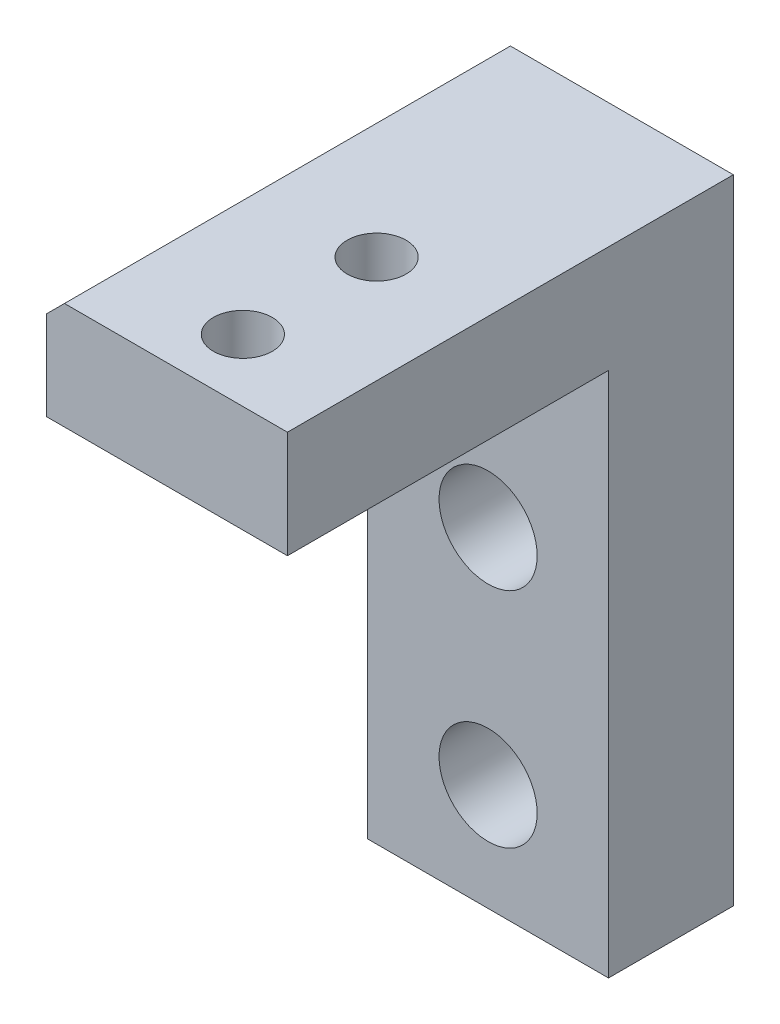
SolidWorks part; units mm, degrees
ref_plane "Front Plane" through (0, 0, 0) normal (0, 0, 1) x (1, 0, 0)
ref_plane "Top Plane" through (0, 0, 0) normal (0, 1, 0) x (1, 0, 0)
ref_plane "Right Plane" through (0, 0, 0) normal (1, 0, 0) x (0, 0, -1)
sketch "Sketch1" plane through (0, 0, 0) normal (0, 0, 1) x (1, 0, 0)
  line L1 (-17.6697, 16.1437) -> (-4.1697, 16.1437)
  line L2 (-17.6697, 16.1437) -> (-17.6697, -19.3563)
  line L3 (-17.6697, -19.3563) -> (-4.1697, -19.3563)
  line L4 (-4.1697, 16.1437) -> (-4.1697, -19.3563)
  circle A0 centre (-10.9197, -13.3563) radius 2.75
  circle A1 centre (-10.9197, -0.8563) radius 2.75
  point P8 (0, 0)
  point P9 (0, 0)
  dimension "D3" = 5.5
  dimension "D4" = 12.5
  dimension "D5" = 6
  dimension "D1" = 35.5
  dimension "D2" = 13.5
extrude "Boss-Extrude1" add sketch "Sketch1" along normal blind 7
sketch "Sketch2" plane through (0, 0, 7) normal (0, 0, 1) x (1, 0, 0)
  line L0 (-4.1697, -19.3563) -> (-4.1697, 16.1437) construction
  line L1 (-17.6697, 16.1437) -> (-4.1697, 16.1437)
  line L2 (-17.6697, 16.1437) -> (-17.6697, 10.1437)
  line L3 (-17.6697, 10.1437) -> (-4.1697, 10.1437)
  line L4 (-4.1697, 16.1437) -> (-4.1697, 10.1437)
  dimension "D1" = 6
extrude "Boss-Extrude2" add sketch "Sketch2" along normal blind 18
chamfer "Chamfer1" distance 1 angle 45 1 edges at (-17.6697, 16.1437, 12.5)
hole_wizard "M4x0.7 Tapped Hole1" positions "Sketch3" profile "Sketch4" tap size "M4x0.7" standard "ANSI Metric" end condition through all
sketch "Sketch3" plane through (0, 16.1437, 0) normal (0, 1, 0) x (1, 0, 0)
  line L0 (-4.1697, 0) -> (-16.6697, 0) construction
  line L1 (-17.6697, -25) -> (-17.6697, 0) construction
  point P0 (-10.1697, -21.5)
  point P2 (-10.1697, -14)
  dimension "D1" = 14
  dimension "D2" = 21.5
  dimension "D3" = 7.5
  dimension "D4" = 7.5
sketch "Sketch4" plane through (-10.1697, 16.1437, 21.5) normal (1, 0, 0) x (0, 0, 1)
  line L0 (0, 0) -> (0, 35.5)
  line L1 (0, 35.5) -> (1.65, 35.5)
  line L2 (1.65, 35.5) -> (1.65, 0)
  line L5 (1.65, 0) -> (0, 0)
  line L11 (0, -6.35) -> (0, 107.95) construction
  dimension "Thru Tap Drill Dia." = 3.3
  dimension "Thru Tap Drill Depth" = 35.5
cosmetic thread "Hole Thread1" parameters "D2"=4
cosmetic thread "Hole Thread2" parameters "D2"=4
